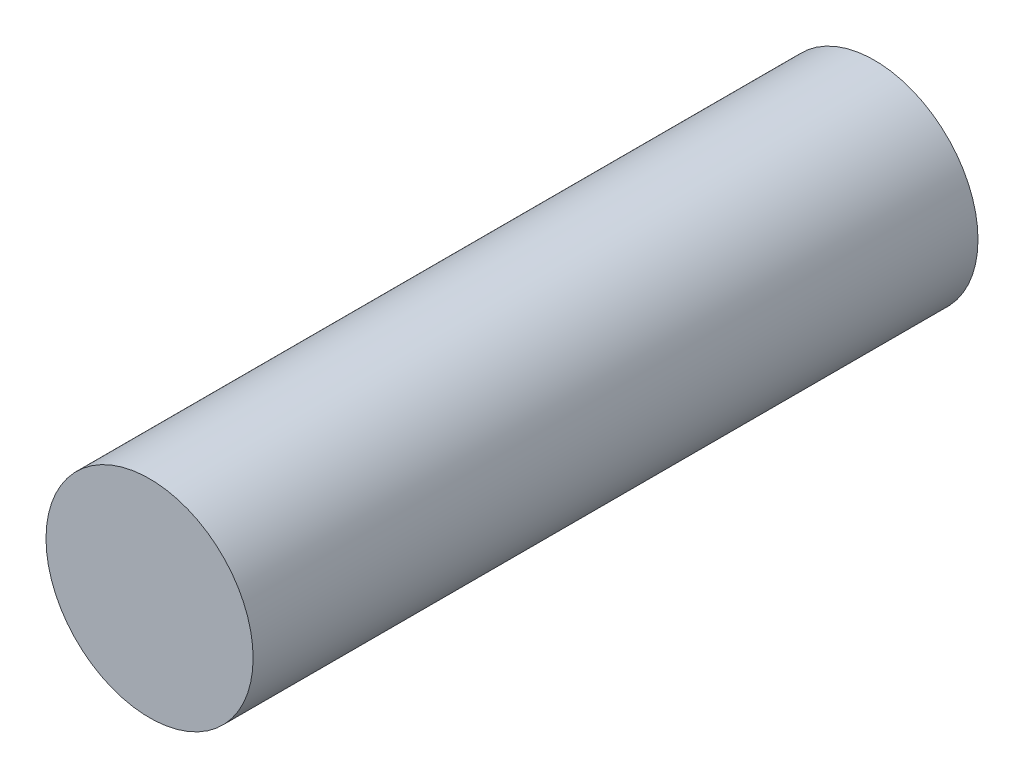
SolidWorks part; units mm, degrees
ref_plane "Front Plane" through (0, 0, 0) normal (0, 0, 1) x (1, 0, 0)
ref_plane "Top Plane" through (0, 0, 0) normal (0, 1, 0) x (1, 0, 0)
ref_plane "Right Plane" through (0, 0, 0) normal (1, 0, 0) x (0, 0, -1)
sketch "Sketch2" plane through (0, 0, 0) normal (0, 0, 1) x (1, 0, 0)
  circle A0 centre (0, 0) radius 5
  dimension "D1" = 10
extrude "Boss-Extrude1" add sketch "Sketch2" along normal blind 35
